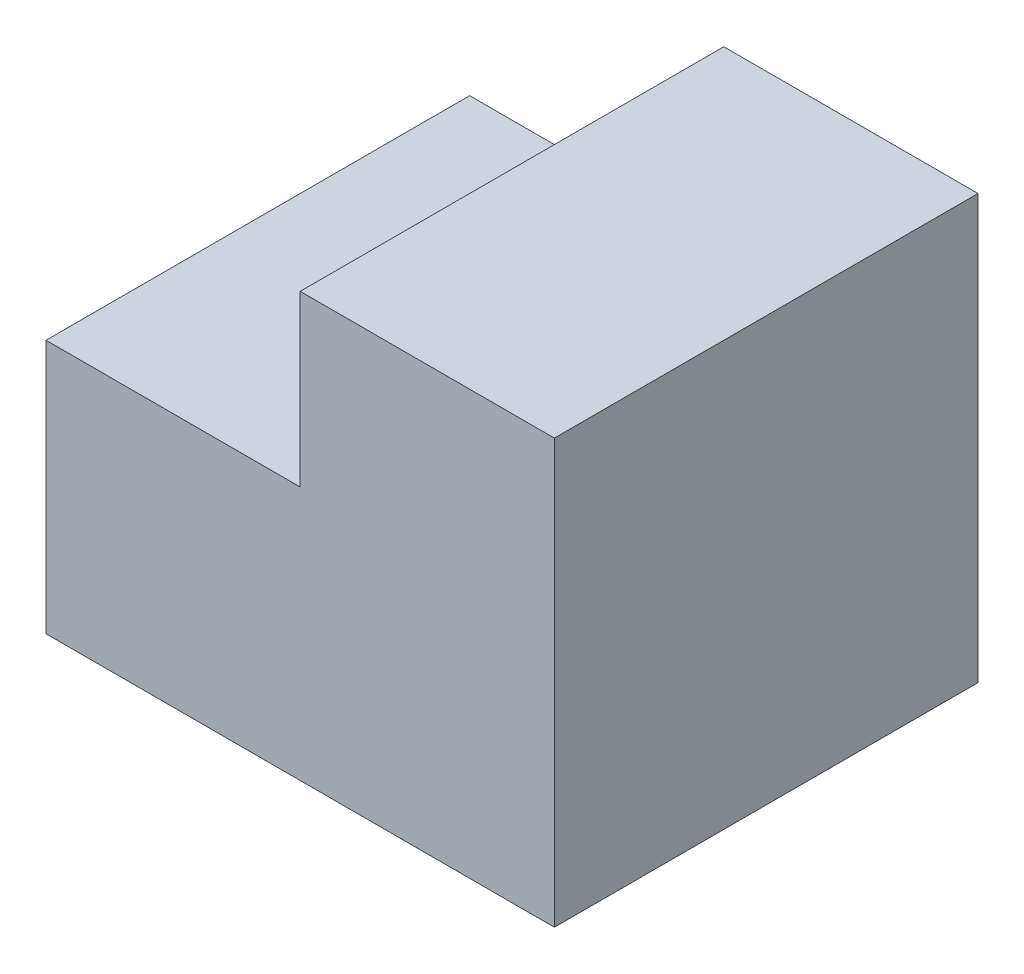
SolidWorks part; units mm, degrees
ref_plane "Front Plane" through (0, 0, 0) normal (0, 0, 1) x (1, 0, 0)
ref_plane "Top Plane" through (0, 0, 0) normal (0, 1, 0) x (1, 0, 0)
ref_plane "Right Plane" through (0, 0, 0) normal (1, 0, 0) x (0, 0, -1)
sketch "Sketch1" plane through (0, 0, 0) normal (0, 0, 1) x (1, 0, 0)
  line L0 (-30, 0) -> (0, 0)
  line L1 (0, 0) -> (0, 25)
  line L2 (0, 25) -> (-15, 25)
  line L3 (-15, 25) -> (-15, 15)
  line L4 (-15, 15) -> (-30, 15)
  line L5 (-30, 15) -> (-30, 0)
  dimension "D1" = 15
  dimension "D2" = 25
  dimension "D3" = 15
  dimension "D4" = 10
extrude "Boss-Extrude1" add sketch "Sketch1" along normal blind 25
